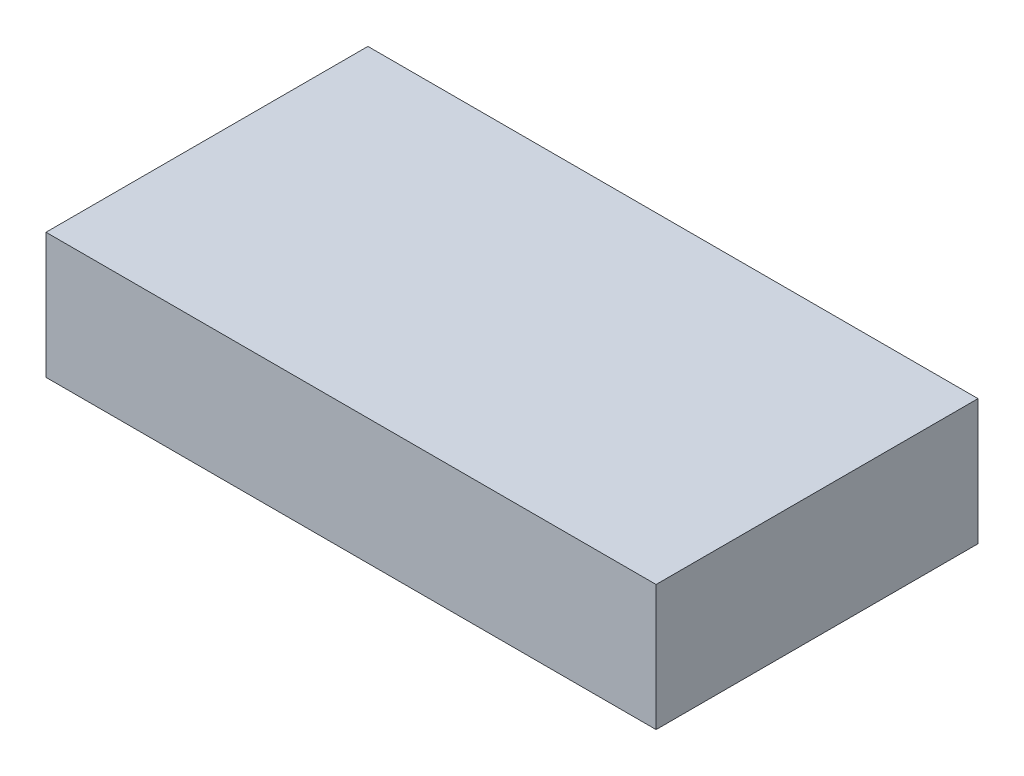
SolidWorks part; units mm, degrees
ref_plane "Płaszczyzna przednia" through (0, 0, 0) normal (0, 0, 1) x (1, 0, 0)
ref_plane "Płaszczyzna górna" through (0, 0, 0) normal (0, 1, 0) x (1, 0, 0)
ref_plane "Płaszczyzna prawa" through (0, 0, 0) normal (1, 0, 0) x (0, 0, -1)
sketch "Sketch1" plane through (0, 0, 0) normal (0, 1, 0) x (1, 0, 0)
  line L1 (-99.5, -52.5) -> (99.5, -52.5)
  line L2 (-99.5, -52.5) -> (-99.5, 52.5)
  line L3 (-99.5, 52.5) -> (99.5, 52.5)
  line L4 (99.5, -52.5) -> (99.5, 52.5)
  line L5 (-99.5, -52.5) -> (99.5, 52.5) construction
  line L6 (-99.5, 52.5) -> (99.5, -52.5) construction
  point P0 (0, 0)
  dimension "D1" = 199
  dimension "D2" = 105
extrude "Boss-Extrude1" add sketch "Sketch1" along normal blind 41
